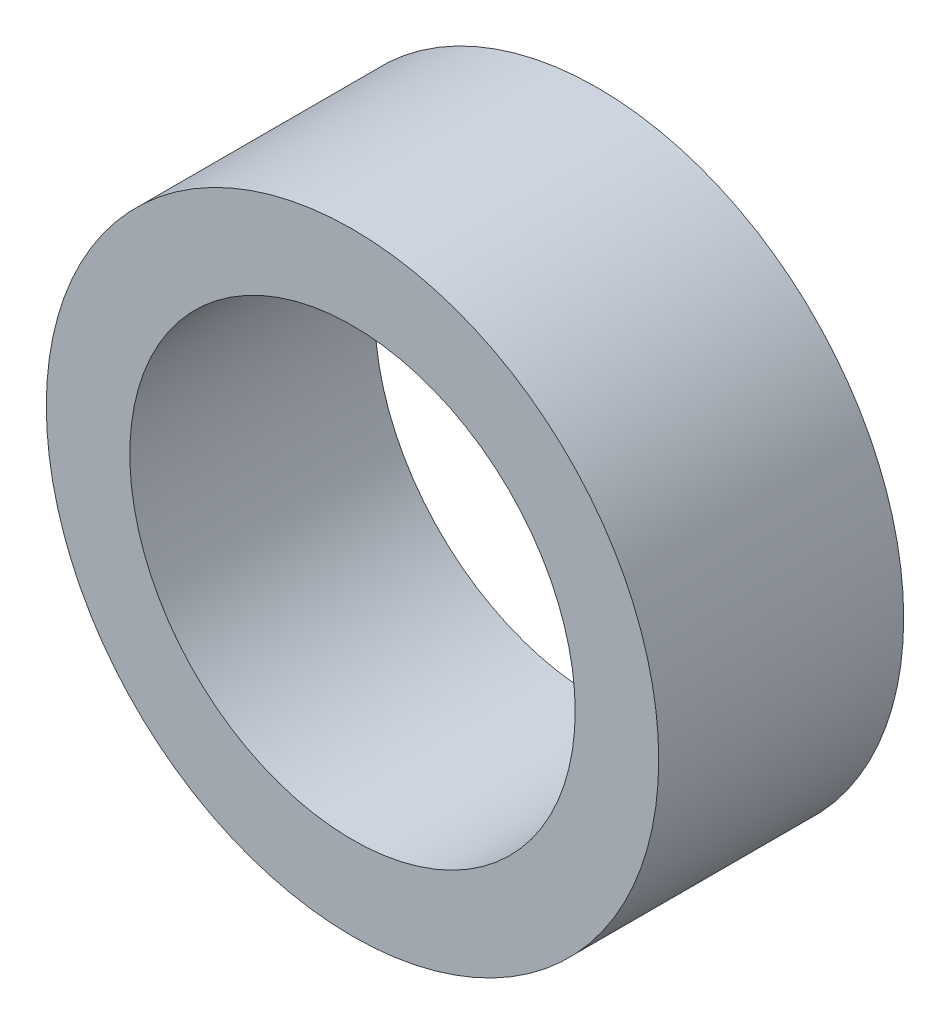
SolidWorks part; units mm, degrees
ref_plane "Front Plane" through (0, 0, 0) normal (0, 0, 1) x (1, 0, 0)
ref_plane "Top Plane" through (0, 0, 0) normal (0, 1, 0) x (1, 0, 0)
ref_plane "Right Plane" through (0, 0, 0) normal (1, 0, 0) x (0, 0, -1)
sketch "Sketch1" plane through (0, 0, 0) normal (0, 0, 1) x (1, 0, 0)
  circle A0 centre (0, 0) radius 8
  circle A1 centre (0, 0) radius 11
  dimension "D1" = 16
  dimension "D2" = 22
extrude "Boss-Extrude1" add sketch "Sketch1" along normal blind 8.8
